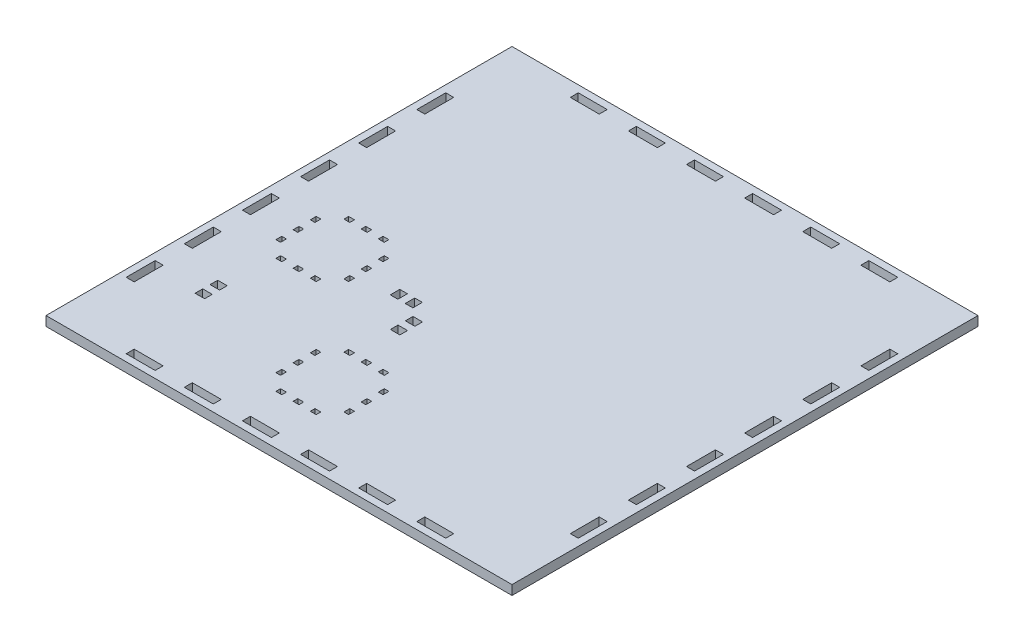
SolidWorks part; units mm, degrees
ref_plane "Front Plane" through (0, 0, 0) normal (0, 0, 1) x (1, 0, 0)
ref_plane "Top Plane" through (0, 0, 0) normal (0, 1, 0) x (1, 0, 0)
ref_plane "Right Plane" through (0, 0, 0) normal (1, 0, 0) x (0, 0, -1)
sketch "Sketch1" plane through (0, 0, 0) normal (0, 1, 0) x (1, 0, 0)
  line L182 (-7.5125, 303.9125) -> (303.8875, 303.9125)
  line L183 (-7.5125, 303.9125) -> (-7.5125, -7.4875)
  line L184 (-7.5125, -7.4875) -> (303.8875, -7.4875)
  line L185 (303.8875, 303.9125) -> (303.8875, -7.4875)
  line L195 (-2.9125, 60.7875) -> (2.4875, 60.7875)
  line L196 (-2.9125, 60.7875) -> (-2.9125, 41.3625)
  line L197 (-2.9125, 41.3625) -> (2.4875, 41.3625)
  line L198 (2.4875, 60.7875) -> (2.4875, 41.3625)
  line L200 (-2.9125, 99.6375) -> (2.4875, 99.6375)
  line L201 (-2.9125, 99.6375) -> (-2.9125, 80.2125)
  line L202 (-2.9125, 80.2125) -> (2.4875, 80.2125)
  line L203 (2.4875, 99.6375) -> (2.4875, 80.2125)
  line L205 (-2.9125, 138.4875) -> (2.4875, 138.4875)
  line L206 (-2.9125, 138.4875) -> (-2.9125, 119.0625)
  line L207 (-2.9125, 119.0625) -> (2.4875, 119.0625)
  line L208 (2.4875, 138.4875) -> (2.4875, 119.0625)
  line L211 (-2.9125, 177.3375) -> (2.4875, 177.3375)
  line L212 (-2.9125, 177.3375) -> (-2.9125, 157.9125)
  line L213 (-2.9125, 157.9125) -> (2.4875, 157.9125)
  line L214 (2.4875, 177.3375) -> (2.4875, 157.9125)
  line L216 (-2.9125, 216.1875) -> (2.4875, 216.1875)
  line L217 (-2.9125, 216.1875) -> (-2.9125, 196.7625)
  line L218 (-2.9125, 196.7625) -> (2.4875, 196.7625)
  line L219 (2.4875, 216.1875) -> (2.4875, 196.7625)
  line L221 (-2.9125, 255.0375) -> (2.4875, 255.0375)
  line L222 (-2.9125, 255.0375) -> (-2.9125, 235.6125)
  line L223 (-2.9125, 235.6125) -> (2.4875, 235.6125)
  line L224 (2.4875, 255.0375) -> (2.4875, 235.6125)
  line L236 (41.3625, 299.3125) -> (60.7875, 299.3125)
  line L237 (41.3625, 299.3125) -> (41.3625, 293.9125)
  line L238 (41.3625, 293.9125) -> (60.7875, 293.9125)
  line L239 (60.7875, 299.3125) -> (60.7875, 293.9125)
  line L241 (80.2125, 299.3125) -> (99.6375, 299.3125)
  line L242 (80.2125, 299.3125) -> (80.2125, 293.9125)
  line L243 (80.2125, 293.9125) -> (99.6375, 293.9125)
  line L244 (99.6375, 299.3125) -> (99.6375, 293.9125)
  line L246 (119.0625, 299.3125) -> (138.4875, 299.3125)
  line L247 (119.0625, 299.3125) -> (119.0625, 293.9125)
  line L248 (119.0625, 293.9125) -> (138.4875, 293.9125)
  line L249 (138.4875, 299.3125) -> (138.4875, 293.9125)
  line L251 (157.9125, 299.3125) -> (177.3375, 299.3125)
  line L252 (157.9125, 299.3125) -> (157.9125, 293.9125)
  line L253 (157.9125, 293.9125) -> (177.3375, 293.9125)
  line L254 (177.3375, 299.3125) -> (177.3375, 293.9125)
  line L256 (196.7625, 299.3125) -> (216.1875, 299.3125)
  line L257 (196.7625, 299.3125) -> (196.7625, 293.9125)
  line L258 (196.7625, 293.9125) -> (216.1875, 293.9125)
  line L259 (216.1875, 299.3125) -> (216.1875, 293.9125)
  line L260 (235.6125, 299.3125) -> (255.0375, 299.3125)
  line L261 (235.6125, 299.3125) -> (235.6125, 293.9125)
  line L262 (235.6125, 293.9125) -> (255.0375, 293.9125)
  line L263 (255.0375, 299.3125) -> (255.0375, 293.9125)
  line L272 (299.2875, 255.0625) -> (293.8875, 255.0625)
  line L273 (299.2875, 255.0625) -> (299.2875, 235.6375)
  line L274 (299.2875, 235.6375) -> (293.8875, 235.6375)
  line L275 (293.8875, 255.0625) -> (293.8875, 235.6375)
  line L276 (299.2875, 216.2125) -> (293.8875, 216.2125)
  line L277 (299.2875, 216.2125) -> (299.2875, 196.7875)
  line L278 (299.2875, 196.7875) -> (293.8875, 196.7875)
  line L279 (293.8875, 216.2125) -> (293.8875, 196.7875)
  line L280 (299.2875, 177.3625) -> (293.8875, 177.3625)
  line L281 (299.2875, 177.3625) -> (299.2875, 157.9375)
  line L282 (299.2875, 157.9375) -> (293.8875, 157.9375)
  line L283 (293.8875, 177.3625) -> (293.8875, 157.9375)
  line L284 (299.2875, 138.5125) -> (293.8875, 138.5125)
  line L285 (299.2875, 138.5125) -> (299.2875, 119.0875)
  line L286 (299.2875, 119.0875) -> (293.8875, 119.0875)
  line L287 (293.8875, 138.5125) -> (293.8875, 119.0875)
  line L288 (299.2875, 99.6625) -> (293.8875, 99.6625)
  line L289 (299.2875, 99.6625) -> (299.2875, 80.2375)
  line L290 (299.2875, 80.2375) -> (293.8875, 80.2375)
  line L291 (293.8875, 99.6625) -> (293.8875, 80.2375)
  line L292 (299.2875, 60.8125) -> (293.8875, 60.8125)
  line L293 (299.2875, 60.8125) -> (299.2875, 41.3875)
  line L294 (299.2875, 41.3875) -> (293.8875, 41.3875)
  line L295 (293.8875, 60.8125) -> (293.8875, 41.3875)
  line L304 (255.0125, 2.5125) -> (235.5875, 2.5125)
  line L305 (255.0125, 2.5125) -> (255.0125, -2.8875)
  line L306 (255.0125, -2.8875) -> (235.5875, -2.8875)
  line L307 (235.5875, 2.5125) -> (235.5875, -2.8875)
  line L308 (216.1625, 2.5125) -> (196.7375, 2.5125)
  line L309 (216.1625, 2.5125) -> (216.1625, -2.8875)
  line L310 (216.1625, -2.8875) -> (196.7375, -2.8875)
  line L311 (196.7375, 2.5125) -> (196.7375, -2.8875)
  line L312 (177.3125, 2.5125) -> (157.8875, 2.5125)
  line L313 (177.3125, 2.5125) -> (177.3125, -2.8875)
  line L314 (177.3125, -2.8875) -> (157.8875, -2.8875)
  line L315 (157.8875, 2.5125) -> (157.8875, -2.8875)
  line L316 (138.4625, 2.5125) -> (119.0375, 2.5125)
  line L317 (138.4625, 2.5125) -> (138.4625, -2.8875)
  line L318 (138.4625, -2.8875) -> (119.0375, -2.8875)
  line L319 (119.0375, 2.5125) -> (119.0375, -2.8875)
  line L320 (99.6125, 2.5125) -> (80.1875, 2.5125)
  line L321 (99.6125, 2.5125) -> (99.6125, -2.8875)
  line L322 (99.6125, -2.8875) -> (80.1875, -2.8875)
  line L323 (80.1875, 2.5125) -> (80.1875, -2.8875)
  line L324 (60.7625, 2.5125) -> (41.3375, 2.5125)
  line L325 (60.7625, 2.5125) -> (60.7625, -2.8875)
  line L326 (60.7625, -2.8875) -> (41.3375, -2.8875)
  line L327 (41.3375, 2.5125) -> (41.3375, -2.8875)
  line L528 (36.1625, 151.0125) -> (40.1625, 151.0125)
  line L529 (36.1625, 151.0125) -> (36.1625, 147.8375)
  line L530 (36.1625, 147.8375) -> (40.1625, 147.8375)
  line L531 (40.1625, 151.0125) -> (40.1625, 147.8375)
  line L532 (47.6625, 151.0125) -> (51.6625, 151.0125)
  line L533 (47.6625, 151.0125) -> (47.6625, 147.8375)
  line L534 (47.6625, 147.8375) -> (51.6625, 147.8375)
  line L535 (51.6625, 151.0125) -> (51.6625, 147.8375)
  line L536 (59.1625, 151.0125) -> (63.1625, 151.0125)
  line L537 (59.1625, 151.0125) -> (59.1625, 147.8375)
  line L538 (59.1625, 147.8375) -> (63.1625, 147.8375)
  line L539 (63.1625, 151.0125) -> (63.1625, 147.8375)
  line L540 (70.8125, 140.1875) -> (73.9875, 140.1875)
  line L541 (70.8125, 140.1875) -> (70.8125, 136.1875)
  line L542 (70.8125, 136.1875) -> (73.9875, 136.1875)
  line L543 (73.9875, 140.1875) -> (73.9875, 136.1875)
  line L544 (70.8125, 128.6875) -> (73.9875, 128.6875)
  line L545 (70.8125, 128.6875) -> (70.8125, 124.6875)
  line L546 (70.8125, 124.6875) -> (73.9875, 124.6875)
  line L547 (73.9875, 128.6875) -> (73.9875, 124.6875)
  line L548 (70.8125, 117.1875) -> (73.9875, 117.1875)
  line L549 (70.8125, 117.1875) -> (70.8125, 113.1875)
  line L550 (70.8125, 113.1875) -> (73.9875, 113.1875)
  line L551 (73.9875, 117.1875) -> (73.9875, 113.1875)
  line L552 (63.1625, 105.5375) -> (59.1625, 105.5375)
  line L553 (63.1625, 105.5375) -> (63.1625, 102.3625)
  line L554 (63.1625, 102.3625) -> (59.1625, 102.3625)
  line L555 (59.1625, 105.5375) -> (59.1625, 102.3625)
  line L556 (51.6625, 105.5375) -> (47.6625, 105.5375)
  line L557 (51.6625, 105.5375) -> (51.6625, 102.3625)
  line L558 (51.6625, 102.3625) -> (47.6625, 102.3625)
  line L559 (47.6625, 105.5375) -> (47.6625, 102.3625)
  line L560 (40.1625, 105.5375) -> (36.1625, 105.5375)
  line L561 (40.1625, 105.5375) -> (40.1625, 102.3625)
  line L562 (40.1625, 102.3625) -> (36.1625, 102.3625)
  line L563 (36.1625, 105.5375) -> (36.1625, 102.3625)
  line L564 (28.5125, 113.1875) -> (25.3375, 113.1875)
  line L565 (28.5125, 113.1875) -> (28.5125, 117.1875)
  line L566 (28.5125, 117.1875) -> (25.3375, 117.1875)
  line L567 (25.3375, 113.1875) -> (25.3375, 117.1875)
  line L568 (28.5125, 124.6875) -> (25.3375, 124.6875)
  line L569 (28.5125, 124.6875) -> (28.5125, 128.6875)
  line L570 (28.5125, 128.6875) -> (25.3375, 128.6875)
  line L571 (25.3375, 124.6875) -> (25.3375, 128.6875)
  line L572 (28.5125, 136.1875) -> (25.3375, 136.1875)
  line L573 (28.5125, 136.1875) -> (28.5125, 140.1875)
  line L574 (28.5125, 140.1875) -> (25.3375, 140.1875)
  line L575 (25.3375, 136.1875) -> (25.3375, 140.1875)
  line L576 (113.1625, 74.0125) -> (117.1625, 74.0125)
  line L577 (113.1625, 74.0125) -> (113.1625, 70.8375)
  line L578 (113.1625, 70.8375) -> (117.1625, 70.8375)
  line L579 (117.1625, 74.0125) -> (117.1625, 70.8375)
  line L580 (124.6625, 74.0125) -> (128.6625, 74.0125)
  line L581 (124.6625, 74.0125) -> (124.6625, 70.8375)
  line L582 (124.6625, 70.8375) -> (128.6625, 70.8375)
  line L583 (128.6625, 74.0125) -> (128.6625, 70.8375)
  line L584 (136.1625, 74.0125) -> (140.1625, 74.0125)
  line L585 (136.1625, 74.0125) -> (136.1625, 70.8375)
  line L586 (136.1625, 70.8375) -> (140.1625, 70.8375)
  line L587 (140.1625, 74.0125) -> (140.1625, 70.8375)
  line L588 (150.9875, 63.1875) -> (147.8125, 63.1875)
  line L589 (150.9875, 63.1875) -> (150.9875, 59.1875)
  line L590 (150.9875, 59.1875) -> (147.8125, 59.1875)
  line L591 (147.8125, 63.1875) -> (147.8125, 59.1875)
  line L592 (150.9875, 51.6875) -> (147.8125, 51.6875)
  line L593 (150.9875, 51.6875) -> (150.9875, 47.6875)
  line L594 (150.9875, 47.6875) -> (147.8125, 47.6875)
  line L595 (147.8125, 51.6875) -> (147.8125, 47.6875)
  line L596 (150.9875, 40.1875) -> (147.8125, 40.1875)
  line L597 (150.9875, 40.1875) -> (150.9875, 36.1875)
  line L598 (150.9875, 36.1875) -> (147.8125, 36.1875)
  line L599 (147.8125, 40.1875) -> (147.8125, 36.1875)
  line L600 (140.1625, 28.5375) -> (136.1625, 28.5375)
  line L601 (140.1625, 28.5375) -> (140.1625, 25.3625)
  line L602 (140.1625, 25.3625) -> (136.1625, 25.3625)
  line L603 (136.1625, 28.5375) -> (136.1625, 25.3625)
  line L604 (128.6625, 28.5375) -> (124.6625, 28.5375)
  line L605 (128.6625, 28.5375) -> (128.6625, 25.3625)
  line L606 (128.6625, 25.3625) -> (124.6625, 25.3625)
  line L607 (124.6625, 28.5375) -> (124.6625, 25.3625)
  line L608 (117.1625, 28.5375) -> (113.1625, 28.5375)
  line L609 (117.1625, 28.5375) -> (117.1625, 25.3625)
  line L610 (117.1625, 25.3625) -> (113.1625, 25.3625)
  line L611 (113.1625, 28.5375) -> (113.1625, 25.3625)
  line L612 (105.5125, 36.1875) -> (102.3375, 36.1875)
  line L613 (105.5125, 36.1875) -> (105.5125, 40.1875)
  line L614 (105.5125, 40.1875) -> (102.3375, 40.1875)
  line L615 (102.3375, 36.1875) -> (102.3375, 40.1875)
  line L616 (105.5125, 47.6875) -> (102.3375, 47.6875)
  line L617 (105.5125, 47.6875) -> (105.5125, 51.6875)
  line L618 (105.5125, 51.6875) -> (102.3375, 51.6875)
  line L619 (102.3375, 47.6875) -> (102.3375, 51.6875)
  line L620 (105.5125, 59.1875) -> (102.3375, 59.1875)
  line L621 (105.5125, 59.1875) -> (105.5125, 63.1875)
  line L622 (105.5125, 63.1875) -> (102.3375, 63.1875)
  line L623 (102.3375, 59.1875) -> (102.3375, 63.1875)
  dimension "D1" = 311.4
  dimension "D3" = 311.4
extrude "Boss-Extrude4" add sketch "Sketch1" along normal blind 6.35
sketch "Sketch4" plane through (0, 6.35, 0) normal (0, 1, 0) x (1, 0, 0)
  line L0 (303.8875, 303.9125) -> (-7.5125, 303.9125) construction
  line B0 (41.3375, 2.5125) -> (60.7625, 2.5125)
  line B1 (2.4875, 2.5125) -> (21.9125, 2.5125)
  line B2 (2.4875, 2.5125) -> (2.4875, -2.8875)
  line B3 (2.4875, -2.8875) -> (21.9125, -2.8875)
  line B4 (21.9125, 2.5125) -> (21.9125, -2.8875)
  line B5 (41.3375, 2.5125) -> (41.3375, -2.8875)
  line B6 (41.3375, -2.8875) -> (60.7625, -2.8875)
  line B7 (60.7625, 2.5125) -> (60.7625, -2.8875)
  line B8 (80.1875, 2.5125) -> (99.6125, 2.5125)
  line B9 (80.1875, 2.5125) -> (80.1875, -2.8875)
  line B10 (80.1875, -2.8875) -> (99.6125, -2.8875)
  line B11 (99.6125, 2.5125) -> (99.6125, -2.8875)
  line B12 (119.0375, 2.5125) -> (138.4625, 2.5125)
  line B13 (119.0375, 2.5125) -> (119.0375, -2.8875)
  line B14 (119.0375, -2.8875) -> (138.4625, -2.8875)
  line B15 (138.4625, 2.5125) -> (138.4625, -2.8875)
  line B16 (157.8875, 2.5125) -> (177.3125, 2.5125)
  line B17 (157.8875, 2.5125) -> (157.8875, -2.8875)
  line B18 (157.8875, -2.8875) -> (177.3125, -2.8875)
  line B19 (177.3125, 2.5125) -> (177.3125, -2.8875)
  line B20 (196.7375, 2.5125) -> (216.1625, 2.5125)
  line B21 (196.7375, 2.5125) -> (196.7375, -2.8875)
  line B22 (196.7375, -2.8875) -> (216.1625, -2.8875)
  line B23 (216.1625, 2.5125) -> (216.1625, -2.8875)
  line B24 (235.5875, 2.5125) -> (255.0125, 2.5125)
  line B25 (235.5875, 2.5125) -> (235.5875, -2.8875)
  line B26 (235.5875, -2.8875) -> (255.0125, -2.8875)
  line B27 (255.0125, 2.5125) -> (255.0125, -2.8875)
  line B28 (274.4375, 2.5125) -> (293.8625, 2.5125)
  line B29 (274.4375, 2.5125) -> (274.4375, -2.8875)
  line B30 (274.4375, -2.8875) -> (293.8625, -2.8875)
  line B31 (293.8625, 2.5125) -> (293.8625, -2.8875)
  line B32 (-2.9125, 60.7875) -> (2.4875, 60.7875)
  line B33 (-2.9125, 2.5125) -> (2.4875, 2.5125)
  line B34 (-2.9125, 2.5125) -> (-2.9125, 21.9375)
  line B35 (-2.9125, 21.9375) -> (2.4875, 21.9375)
  line B36 (2.4875, 2.5125) -> (2.4875, 21.9375)
  line B37 (2.4875, 41.3625) -> (2.4875, 60.7875)
  line B38 (-2.9125, 41.3625) -> (-2.9125, 60.7875)
  line B39 (-2.9125, 41.3625) -> (2.4875, 41.3625)
  line B40 (-2.9125, 99.6375) -> (2.4875, 99.6375)
  line B41 (2.4875, 80.2125) -> (2.4875, 99.6375)
  line B42 (-2.9125, 80.2125) -> (-2.9125, 99.6375)
  line B43 (-2.9125, 80.2125) -> (2.4875, 80.2125)
  line B44 (-2.9125, 138.4875) -> (2.4875, 138.4875)
  line B45 (2.4875, 119.0625) -> (2.4875, 138.4875)
  line B46 (-2.9125, 119.0625) -> (-2.9125, 138.4875)
  line B47 (-2.9125, 119.0625) -> (2.4875, 119.0625)
  line B48 (-2.9125, 177.3375) -> (2.4875, 177.3375)
  line B49 (2.4875, 157.9125) -> (2.4875, 177.3375)
  line B50 (-2.9125, 157.9125) -> (-2.9125, 177.3375)
  line B51 (-2.9125, 157.9125) -> (2.4875, 157.9125)
  line B52 (-2.9125, 216.1875) -> (2.4875, 216.1875)
  line B53 (2.4875, 196.7625) -> (2.4875, 216.1875)
  line B54 (-2.9125, 196.7625) -> (-2.9125, 216.1875)
  line B55 (-2.9125, 196.7625) -> (2.4875, 196.7625)
  line B56 (-2.9125, 255.0375) -> (2.4875, 255.0375)
  line B57 (2.4875, 235.6125) -> (2.4875, 255.0375)
  line B58 (-2.9125, 235.6125) -> (-2.9125, 255.0375)
  line B59 (-2.9125, 235.6125) -> (2.4875, 235.6125)
  line B60 (-2.9125, 293.8875) -> (2.4875, 293.8875)
  line B61 (2.4875, 274.4625) -> (2.4875, 293.8875)
  line B62 (-2.9125, 274.4625) -> (-2.9125, 293.8875)
  line B63 (-2.9125, 274.4625) -> (2.4875, 274.4625)
  line B64 (-7.5125, 303.9125) -> (303.8875, -7.4875) construction
  line B65 (21.9375, 299.3125) -> (21.9375, 293.9125)
  line B66 (21.9375, 299.3125) -> (2.5125, 299.3125)
  line B67 (21.9375, 293.9125) -> (2.5125, 293.9125)
  line B68 (2.5125, 299.3125) -> (2.5125, 293.9125)
  line B69 (60.7875, 299.3125) -> (60.7875, 293.9125)
  line B70 (60.7875, 299.3125) -> (41.3625, 299.3125)
  line B71 (60.7875, 293.9125) -> (41.3625, 293.9125)
  line B72 (41.3625, 299.3125) -> (41.3625, 293.9125)
  line B73 (99.6375, 299.3125) -> (99.6375, 293.9125)
  line B74 (99.6375, 299.3125) -> (80.2125, 299.3125)
  line B75 (99.6375, 293.9125) -> (80.2125, 293.9125)
  line B76 (80.2125, 299.3125) -> (80.2125, 293.9125)
  line B77 (138.4875, 299.3125) -> (138.4875, 293.9125)
  line B78 (138.4875, 299.3125) -> (119.0625, 299.3125)
  line B79 (138.4875, 293.9125) -> (119.0625, 293.9125)
  line B80 (119.0625, 299.3125) -> (119.0625, 293.9125)
  line B81 (177.3375, 299.3125) -> (177.3375, 293.9125)
  line B82 (177.3375, 299.3125) -> (157.9125, 299.3125)
  line B83 (177.3375, 293.9125) -> (157.9125, 293.9125)
  line B84 (157.9125, 299.3125) -> (157.9125, 293.9125)
  line B85 (216.1875, 299.3125) -> (216.1875, 293.9125)
  line B86 (216.1875, 299.3125) -> (196.7625, 299.3125)
  line B87 (216.1875, 293.9125) -> (196.7625, 293.9125)
  line B88 (196.7625, 299.3125) -> (196.7625, 293.9125)
  line B89 (255.0375, 299.3125) -> (255.0375, 293.9125)
  line B90 (255.0375, 299.3125) -> (235.6125, 299.3125)
  line B91 (255.0375, 293.9125) -> (235.6125, 293.9125)
  line B92 (293.8875, 293.9125) -> (274.4625, 293.9125)
  line B93 (274.4625, 299.3125) -> (274.4625, 293.9125)
  line B94 (293.8875, 299.3125) -> (274.4625, 299.3125)
  line B95 (293.8875, 299.3125) -> (293.8875, 293.9125)
  line B96 (235.6125, 299.3125) -> (235.6125, 293.9125)
  line B97 (293.8875, 2.5375) -> (299.2875, 2.5375)
  line B98 (299.2875, 21.9625) -> (299.2875, 2.5375)
  line B99 (293.8875, 21.9625) -> (299.2875, 21.9625)
  line B100 (293.8875, 21.9625) -> (293.8875, 2.5375)
  line B101 (293.8875, 41.3875) -> (299.2875, 41.3875)
  line B102 (299.2875, 60.8125) -> (299.2875, 41.3875)
  line B103 (293.8875, 60.8125) -> (299.2875, 60.8125)
  line B104 (293.8875, 60.8125) -> (293.8875, 41.3875)
  line B105 (293.8875, 80.2375) -> (299.2875, 80.2375)
  line B106 (299.2875, 99.6625) -> (299.2875, 80.2375)
  line B107 (293.8875, 99.6625) -> (299.2875, 99.6625)
  line B108 (293.8875, 99.6625) -> (293.8875, 80.2375)
  line B109 (293.8875, 119.0875) -> (299.2875, 119.0875)
  line B110 (299.2875, 138.5125) -> (299.2875, 119.0875)
  line B111 (293.8875, 138.5125) -> (299.2875, 138.5125)
  line B112 (293.8875, 138.5125) -> (293.8875, 119.0875)
  line B113 (293.8875, 157.9375) -> (299.2875, 157.9375)
  line B114 (299.2875, 177.3625) -> (299.2875, 157.9375)
  line B115 (293.8875, 177.3625) -> (299.2875, 177.3625)
  line B116 (293.8875, 177.3625) -> (293.8875, 157.9375)
  line B117 (293.8875, 196.7875) -> (299.2875, 196.7875)
  line B118 (299.2875, 216.2125) -> (299.2875, 196.7875)
  line B119 (293.8875, 216.2125) -> (299.2875, 216.2125)
  line B120 (293.8875, 216.2125) -> (293.8875, 196.7875)
  line B121 (293.8875, 235.6375) -> (299.2875, 235.6375)
  line B122 (299.2875, 255.0625) -> (299.2875, 235.6375)
  line B123 (293.8875, 255.0625) -> (299.2875, 255.0625)
  line B124 (293.8875, 274.4875) -> (299.2875, 274.4875)
  line B125 (299.2875, 293.9125) -> (299.2875, 274.4875)
  line B126 (293.8875, 293.9125) -> (299.2875, 293.9125)
  line B127 (293.8875, 293.9125) -> (293.8875, 274.4875)
  line B128 (293.8875, 255.0625) -> (293.8875, 235.6375)
  line B129 (2.5125, 293.9125) -> (2.4875, 293.8875)
  line B130 (293.8875, 2.5375) -> (293.8625, 2.5125)
  line B131 (35.6625, 260.7375) -> (115.6625, 260.7375)
  line B132 (35.6625, 260.7375) -> (35.6625, 180.7375)
  line B133 (35.6625, 180.7375) -> (115.6625, 180.7375)
  line B134 (115.6625, 260.7375) -> (115.6625, 180.7375)
  arc B135 (-2.9125, 293.8875) -> (2.5125, 299.2874) centre (2.4875, 293.8875) cw
  arc B136 (293.8625, -2.8875) -> (299.2624, 2.5375) centre (293.8625, 2.5125) ccw
  arc B137 (299.2875, 293.9125) -> (293.8875, 299.3125) centre (293.8875, 293.9125) ccw
  arc B138 (2.4875, -2.8875) -> (-2.9125, 2.5125) centre (2.4875, 2.5125) cw
sketch_block_instance "Outer Mounting Holes-4"
sketch_block "Outer Mounting Holes" parameters "D1"=5.4, "D2"=19.425, "D3"=19.425, "D4"=19.425, "D5"=80, "D6"=302.2
extrude "Cut-Extrude3" cut sketch "Sketch4" against normal blind 6.35 contours B66 B68 B67 B65 | B62 B63 B61 B60 | B135 B60 B129 B68 | B126 B137 B95 | B95 B94 B93 B92 | B126 B127 B124 B125 | B33 B36 B35 B34 | B4 B1 B2 B3 | B138 B2 B33 | B31 B136 B97 B130 | B31 B28 B29 B30 | B99 B100 B97 B98
sketch "Sketch5" plane through (0, 6.35, 0) normal (0, 1, 0) x (1, 0, 0)
  line L8 (254.9969, 293.9531) -> (254.9969, 299.2719)
  line L9 (235.6531, 293.9531) -> (254.9969, 293.9531)
  line L10 (235.6531, 299.2719) -> (235.6531, 293.9531)
  line L11 (254.9969, 299.2719) -> (235.6531, 299.2719)
  line L12 (254.9969, 293.9531) -> (254.9969, 299.2719)
  line L13 (235.6531, 293.9531) -> (254.9969, 293.9531)
  line L14 (235.6531, 299.2719) -> (235.6531, 293.9531)
  line L15 (254.9969, 299.2719) -> (235.6531, 299.2719)
  line L16 (-7.5531, -7.5281) -> (303.9281, -7.5281)
  line L17 (303.9281, -7.5281) -> (303.9281, 303.9531)
  line L18 (-7.5531, 303.9531) -> (-7.5531, -7.5281)
  line L19 (303.9281, 303.9531) -> (-7.5531, 303.9531)
  line L20 (-7.5531, -7.5281) -> (303.9281, -7.5281)
  line L21 (303.9281, -7.5281) -> (303.9281, 303.9531)
  line L22 (-7.5531, 303.9531) -> (-7.5531, -7.5281)
  line L23 (303.9281, 303.9531) -> (-7.5531, 303.9531)
  line L24 (293.8625, -2.8469) -> (274.4781, -2.8469)
  line L25 (274.4781, -2.8469) -> (274.4781, 2.4719)
  line L26 (274.4781, 2.4719) -> (293.8625, 2.4719)
  line L27 (293.8625, -2.8469) -> (274.4781, -2.8469)
  line L28 (274.5031, 299.2719) -> (293.8875, 299.2719)
  line L29 (274.5031, 293.9531) -> (274.5031, 299.2719)
  line L30 (293.8875, 293.9531) -> (274.5031, 293.9531)
  line L31 (274.5031, 299.2719) -> (293.8875, 299.2719)
  line L32 (274.5031, 293.9531) -> (274.5031, 299.2719)
  line L33 (293.8875, 293.9531) -> (274.5031, 293.9531)
  line L34 (299.2469, 41.4281) -> (299.2469, 60.7719)
  line L35 (293.9281, 196.8281) -> (299.2469, 196.8281)
  line L36 (293.9281, 216.1719) -> (293.9281, 196.8281)
  line L37 (299.2469, 196.8281) -> (299.2469, 216.1719)
  line L38 (299.2469, 216.1719) -> (293.9281, 216.1719)
  line L39 (293.9281, 196.8281) -> (299.2469, 196.8281)
  line L40 (293.9281, 274.5281) -> (299.2469, 274.5281)
  line L41 (299.2469, 274.5281) -> (299.2469, 293.9125)
  line L42 (293.9281, 293.9125) -> (293.9281, 274.5281)
  line L43 (293.9281, 274.5281) -> (299.2469, 274.5281)
  line L44 (299.2469, 274.5281) -> (299.2469, 293.9125)
  line L45 (293.9281, 293.9125) -> (293.9281, 274.5281)
  line L46 (293.9281, 216.1719) -> (293.9281, 196.8281)
  line L47 (299.2469, 196.8281) -> (299.2469, 216.1719)
  line L48 (299.2469, 216.1719) -> (293.9281, 216.1719)
  line L49 (293.9281, 41.4281) -> (299.2469, 41.4281)
  line L50 (293.9281, 60.7719) -> (293.9281, 41.4281)
  line L51 (299.2469, 60.7719) -> (293.9281, 60.7719)
  line L52 (299.2469, 41.4281) -> (299.2469, 60.7719)
  line L53 (293.9281, 41.4281) -> (299.2469, 41.4281)
  line L54 (293.9281, 60.7719) -> (293.9281, 41.4281)
  line L55 (299.2469, 60.7719) -> (293.9281, 60.7719)
  line L56 (274.4781, -2.8469) -> (274.4781, 2.4719)
  line L57 (293.9281, 235.6781) -> (299.2469, 235.6781)
  line L58 (299.2469, 235.6781) -> (299.2469, 255.0219)
  line L59 (299.2469, 255.0219) -> (293.9281, 255.0219)
  line L60 (293.9281, 255.0219) -> (293.9281, 235.6781)
  line L61 (293.9281, 235.6781) -> (299.2469, 235.6781)
  line L62 (299.2469, 235.6781) -> (299.2469, 255.0219)
  line L63 (299.2469, 255.0219) -> (293.9281, 255.0219)
  line L64 (293.9281, 255.0219) -> (293.9281, 235.6781)
  line L65 (274.4781, 2.4719) -> (293.8625, 2.4719)
  line L70 (299.2469, 157.9781) -> (299.2469, 177.3219)
  line L71 (293.9281, 177.3219) -> (293.9281, 157.9781)
  line L72 (293.9281, 157.9781) -> (299.2469, 157.9781)
  line L73 (21.8969, 293.9531) -> (21.8969, 299.2719)
  line L74 (2.5125, 293.9531) -> (21.8969, 293.9531)
  line L75 (21.8969, 299.2719) -> (2.5125, 299.2719)
  line L76 (21.8969, 293.9531) -> (21.8969, 299.2719)
  line L77 (2.5125, 293.9531) -> (21.8969, 293.9531)
  line L78 (21.8969, 299.2719) -> (2.5125, 299.2719)
  line L79 (299.2469, 177.3219) -> (293.9281, 177.3219)
  line L80 (299.2469, 157.9781) -> (299.2469, 177.3219)
  line L81 (293.9281, 177.3219) -> (293.9281, 157.9781)
  line L82 (293.9281, 157.9781) -> (299.2469, 157.9781)
  line L83 (299.2469, 177.3219) -> (293.9281, 177.3219)
  line L85 (-2.8719, 274.5031) -> (2.4469, 274.5031)
  line L86 (-2.8719, 293.8875) -> (-2.8719, 274.5031)
  line L87 (2.4469, 274.5031) -> (2.4469, 293.8875)
  line L88 (-2.8719, 274.5031) -> (2.4469, 274.5031)
  line L89 (-2.8719, 293.8875) -> (-2.8719, 274.5031)
  line L90 (2.4469, 274.5031) -> (2.4469, 293.8875)
  line L91 (-2.8719, 157.9531) -> (2.4469, 157.9531)
  line L92 (216.1219, -2.8469) -> (216.1219, 2.4719)
  line L93 (-2.8719, 177.2969) -> (-2.8719, 157.9531)
  line L94 (196.7781, 2.4719) -> (196.7781, -2.8469)
  line L95 (196.7781, -2.8469) -> (216.1219, -2.8469)
  line L96 (216.1219, 2.4719) -> (196.7781, 2.4719)
  line L97 (254.9719, -2.8469) -> (254.9719, 2.4719)
  line L98 (235.6281, 2.4719) -> (235.6281, -2.8469)
  line L99 (235.6281, -2.8469) -> (254.9719, -2.8469)
  line L100 (299.2469, 119.1281) -> (299.2469, 138.4719)
  line L101 (293.9281, 138.4719) -> (293.9281, 119.1281)
  line L102 (60.7469, 293.9531) -> (60.7469, 299.2719)
  line L103 (41.4031, 293.9531) -> (60.7469, 293.9531)
  line L104 (41.4031, 299.2719) -> (41.4031, 293.9531)
  line L105 (60.7469, 299.2719) -> (41.4031, 299.2719)
  line L106 (60.7469, 293.9531) -> (60.7469, 299.2719)
  line L107 (41.4031, 293.9531) -> (60.7469, 293.9531)
  line L108 (41.4031, 299.2719) -> (41.4031, 293.9531)
  line L109 (60.7469, 299.2719) -> (41.4031, 299.2719)
  line L110 (293.9281, 119.1281) -> (299.2469, 119.1281)
  line L111 (299.2469, 138.4719) -> (293.9281, 138.4719)
  line L112 (299.2469, 119.1281) -> (299.2469, 138.4719)
  line L113 (293.9281, 138.4719) -> (293.9281, 119.1281)
  line L114 (293.9281, 119.1281) -> (299.2469, 119.1281)
  line L115 (299.2469, 138.4719) -> (293.9281, 138.4719)
  line L116 (254.9719, 2.4719) -> (235.6281, 2.4719)
  line L117 (254.9719, -2.8469) -> (254.9719, 2.4719)
  line L118 (235.6281, 2.4719) -> (235.6281, -2.8469)
  line L119 (235.6281, -2.8469) -> (254.9719, -2.8469)
  line L120 (254.9719, 2.4719) -> (235.6281, 2.4719)
  line L121 (216.1219, -2.8469) -> (216.1219, 2.4719)
  line L122 (196.7781, 2.4719) -> (196.7781, -2.8469)
  line L123 (196.7781, -2.8469) -> (216.1219, -2.8469)
  line L124 (99.5969, 293.9531) -> (99.5969, 299.2719)
  line L125 (80.2531, 299.2719) -> (80.2531, 293.9531)
  line L126 (80.2531, 293.9531) -> (99.5969, 293.9531)
  line L127 (99.5969, 299.2719) -> (80.2531, 299.2719)
  line L128 (99.5969, 293.9531) -> (99.5969, 299.2719)
  line L129 (80.2531, 299.2719) -> (80.2531, 293.9531)
  line L130 (80.2531, 293.9531) -> (99.5969, 293.9531)
  line L131 (99.5969, 299.2719) -> (80.2531, 299.2719)
  line L132 (216.1219, 2.4719) -> (196.7781, 2.4719)
  line L133 (2.4469, 157.9531) -> (2.4469, 177.2969)
  line L134 (299.2469, 80.2781) -> (299.2469, 99.6219)
  line L135 (293.9281, 80.2781) -> (299.2469, 80.2781)
  line L136 (293.9281, 99.6219) -> (293.9281, 80.2781)
  line L137 (299.2469, 99.6219) -> (293.9281, 99.6219)
  line L138 (299.2469, 80.2781) -> (299.2469, 99.6219)
  line L139 (293.9281, 80.2781) -> (299.2469, 80.2781)
  line L140 (293.9281, 99.6219) -> (293.9281, 80.2781)
  line L141 (299.2469, 99.6219) -> (293.9281, 99.6219)
  line L142 (119.1031, 299.2719) -> (119.1031, 293.9531)
  line L143 (138.4469, 293.9531) -> (138.4469, 299.2719)
  line L144 (119.1031, 293.9531) -> (138.4469, 293.9531)
  line L145 (138.4469, 299.2719) -> (119.1031, 299.2719)
  line L146 (119.1031, 299.2719) -> (119.1031, 293.9531)
  line L147 (138.4469, 293.9531) -> (138.4469, 299.2719)
  line L148 (119.1031, 293.9531) -> (138.4469, 293.9531)
  line L149 (138.4469, 299.2719) -> (119.1031, 299.2719)
  line L150 (2.4469, 177.2969) -> (-2.8719, 177.2969)
  line L151 (-2.8719, 157.9531) -> (2.4469, 157.9531)
  line L152 (-2.8719, 177.2969) -> (-2.8719, 157.9531)
  line L153 (2.4469, 157.9531) -> (2.4469, 177.2969)
  line L154 (2.4469, 177.2969) -> (-2.8719, 177.2969)
  line L155 (-2.8719, 235.6531) -> (2.4469, 235.6531)
  line L156 (2.4469, 235.6531) -> (2.4469, 254.9969)
  line L157 (-2.8719, 254.9969) -> (-2.8719, 235.6531)
  line L158 (2.4469, 254.9969) -> (-2.8719, 254.9969)
  line L159 (177.2719, -2.8469) -> (177.2719, 2.4719)
  line L160 (157.9531, 299.2719) -> (157.9531, 293.9531)
  line L161 (177.2969, 293.9531) -> (177.2969, 299.2719)
  line L162 (157.9531, 293.9531) -> (177.2969, 293.9531)
  line L163 (177.2969, 299.2719) -> (157.9531, 299.2719)
  line L164 (157.9531, 299.2719) -> (157.9531, 293.9531)
  line L165 (177.2969, 293.9531) -> (177.2969, 299.2719)
  line L166 (157.9531, 293.9531) -> (177.2969, 293.9531)
  line L167 (177.2969, 299.2719) -> (157.9531, 299.2719)
  line L168 (157.9281, 2.4719) -> (157.9281, -2.8469)
  line L169 (157.9281, -2.8469) -> (177.2719, -2.8469)
  line L170 (299.2469, 2.5375) -> (299.2469, 21.9219)
  line L171 (299.2469, 21.9219) -> (293.9281, 21.9219)
  line L172 (293.9281, 21.9219) -> (293.9281, 2.5375)
  line L173 (299.2469, 2.5375) -> (299.2469, 21.9219)
  line L174 (299.2469, 21.9219) -> (293.9281, 21.9219)
  line L175 (293.9281, 21.9219) -> (293.9281, 2.5375)
  line L176 (177.2719, 2.4719) -> (157.9281, 2.4719)
  line L177 (177.2719, -2.8469) -> (177.2719, 2.4719)
  line L178 (157.9281, 2.4719) -> (157.9281, -2.8469)
  line L179 (157.9281, -2.8469) -> (177.2719, -2.8469)
  line L180 (196.8031, 299.2719) -> (196.8031, 293.9531)
  line L181 (216.1469, 293.9531) -> (216.1469, 299.2719)
  line L182 (216.1469, 299.2719) -> (196.8031, 299.2719)
  line L183 (196.8031, 293.9531) -> (216.1469, 293.9531)
  line L184 (196.8031, 299.2719) -> (196.8031, 293.9531)
  line L185 (216.1469, 293.9531) -> (216.1469, 299.2719)
  line L186 (216.1469, 299.2719) -> (196.8031, 299.2719)
  line L187 (196.8031, 293.9531) -> (216.1469, 293.9531)
  line L188 (177.2719, 2.4719) -> (157.9281, 2.4719)
  line L189 (-2.8719, 235.6531) -> (2.4469, 235.6531)
  line L190 (2.4469, 235.6531) -> (2.4469, 254.9969)
  line L194 (-2.8719, 254.9969) -> (-2.8719, 235.6531)
  line L195 (-2.8719, 196.8031) -> (2.4469, 196.8031)
  line L196 (2.4469, 196.8031) -> (2.4469, 216.1469)
  line L197 (-2.8719, 216.1469) -> (-2.8719, 196.8031)
  line L198 (2.4469, 216.1469) -> (-2.8719, 216.1469)
  line L199 (138.4219, 2.4719) -> (119.0781, 2.4719)
  line L200 (119.0781, -2.8469) -> (138.4219, -2.8469)
  line L201 (138.4219, -2.8469) -> (138.4219, 2.4719)
  line L202 (119.0781, 2.4719) -> (119.0781, -2.8469)
  line L203 (138.4219, 2.4719) -> (119.0781, 2.4719)
  line L204 (119.0781, -2.8469) -> (138.4219, -2.8469)
  line L205 (138.4219, -2.8469) -> (138.4219, 2.4719)
  line L206 (119.0781, 2.4719) -> (119.0781, -2.8469)
  line L207 (-2.8719, 196.8031) -> (2.4469, 196.8031)
  line L208 (2.4469, 196.8031) -> (2.4469, 216.1469)
  line L209 (-2.8719, 216.1469) -> (-2.8719, 196.8031)
  line L210 (2.4469, 216.1469) -> (-2.8719, 216.1469)
  line L211 (2.4469, 254.9969) -> (-2.8719, 254.9969)
  line L212 (51.6219, 147.8781) -> (51.6219, 150.9719)
  line L213 (47.7031, 147.8781) -> (51.6219, 147.8781)
  line L214 (47.7031, 150.9719) -> (47.7031, 147.8781)
  line L215 (51.6219, 150.9719) -> (47.7031, 150.9719)
  line L216 (51.6219, 147.8781) -> (51.6219, 150.9719)
  line L217 (80.2281, 2.4719) -> (80.2281, -2.8469)
  line L218 (99.5719, -2.8469) -> (99.5719, 2.4719)
  line L219 (80.2281, -2.8469) -> (99.5719, -2.8469)
  line L220 (99.5719, 2.4719) -> (80.2281, 2.4719)
  line L221 (80.2281, 2.4719) -> (80.2281, -2.8469)
  line L222 (99.5719, -2.8469) -> (99.5719, 2.4719)
  line L223 (80.2281, -2.8469) -> (99.5719, -2.8469)
  line L224 (99.5719, 2.4719) -> (80.2281, 2.4719)
  line L225 (47.7031, 147.8781) -> (51.6219, 147.8781)
  line L226 (47.7031, 150.9719) -> (47.7031, 147.8781)
  line L227 (51.6219, 150.9719) -> (47.7031, 150.9719)
  line L228 (63.1219, 147.8781) -> (63.1219, 150.9719)
  line L229 (59.2031, 147.8781) -> (63.1219, 147.8781)
  line L230 (59.2031, 150.9719) -> (59.2031, 147.8781)
  line L231 (63.1219, 150.9719) -> (59.2031, 150.9719)
  line L232 (63.1219, 147.8781) -> (63.1219, 150.9719)
  line L233 (59.2031, 147.8781) -> (63.1219, 147.8781)
  line L234 (59.2031, 150.9719) -> (59.2031, 147.8781)
  line L235 (41.3781, 2.4719) -> (41.3781, -2.8469)
  line L236 (60.7219, -2.8469) -> (60.7219, 2.4719)
  line L237 (41.3781, -2.8469) -> (60.7219, -2.8469)
  line L238 (60.7219, 2.4719) -> (41.3781, 2.4719)
  line L239 (41.3781, 2.4719) -> (41.3781, -2.8469)
  line L240 (60.7219, -2.8469) -> (60.7219, 2.4719)
  line L241 (41.3781, -2.8469) -> (60.7219, -2.8469)
  line L242 (60.7219, 2.4719) -> (41.3781, 2.4719)
  line L243 (63.1219, 150.9719) -> (59.2031, 150.9719)
  line L248 (21.8719, 2.4719) -> (21.8719, -2.8469)
  line L249 (21.8719, -2.8469) -> (2.4875, -2.8469)
  line L250 (2.4875, 2.4719) -> (21.8719, 2.4719)
  line L251 (21.8719, 2.4719) -> (21.8719, -2.8469)
  line L252 (21.8719, -2.8469) -> (2.4875, -2.8469)
  line L253 (2.4875, 2.4719) -> (21.8719, 2.4719)
  line L260 (2.4469, 21.8969) -> (2.4469, 2.5125)
  line L261 (-2.8719, 2.5125) -> (-2.8719, 21.8969)
  line L262 (-2.8719, 21.8969) -> (2.4469, 21.8969)
  line L263 (2.4469, 21.8969) -> (2.4469, 2.5125)
  line L264 (-2.8719, 2.5125) -> (-2.8719, 21.8969)
  line L265 (-2.8719, 21.8969) -> (2.4469, 21.8969)
  line L266 (40.1219, 147.8781) -> (40.1219, 150.9719)
  line L267 (36.2031, 147.8781) -> (40.1219, 147.8781)
  line L268 (36.2031, 150.9719) -> (36.2031, 147.8781)
  line L269 (40.1219, 150.9719) -> (36.2031, 150.9719)
  line L270 (40.1219, 147.8781) -> (40.1219, 150.9719)
  line L271 (36.2031, 147.8781) -> (40.1219, 147.8781)
  line L272 (36.2031, 150.9719) -> (36.2031, 147.8781)
  line L273 (40.1219, 150.9719) -> (36.2031, 150.9719)
  line L277 (-2.8719, 41.4031) -> (2.4469, 41.4031)
  line L278 (2.4469, 41.4031) -> (2.4469, 60.7469)
  line L279 (-2.8719, 60.7469) -> (-2.8719, 41.4031)
  line L280 (2.4469, 60.7469) -> (-2.8719, 60.7469)
  line L281 (-2.8719, 41.4031) -> (2.4469, 41.4031)
  line L282 (2.4469, 41.4031) -> (2.4469, 60.7469)
  line L283 (-2.8719, 60.7469) -> (-2.8719, 41.4031)
  line L284 (2.4469, 60.7469) -> (-2.8719, 60.7469)
  line L292 (28.4719, 136.2281) -> (28.4719, 140.1469)
  line L293 (25.3781, 140.1469) -> (25.3781, 136.2281)
  line L294 (25.3781, 136.2281) -> (28.4719, 136.2281)
  line L295 (-2.8719, 80.2531) -> (2.4469, 80.2531)
  line L296 (-2.8719, 99.5969) -> (-2.8719, 80.2531)
  line L297 (2.4469, 80.2531) -> (2.4469, 99.5969)
  line L298 (2.4469, 99.5969) -> (-2.8719, 99.5969)
  line L299 (-2.8719, 80.2531) -> (2.4469, 80.2531)
  line L300 (-2.8719, 99.5969) -> (-2.8719, 80.2531)
  line L301 (2.4469, 80.2531) -> (2.4469, 99.5969)
  line L302 (2.4469, 99.5969) -> (-2.8719, 99.5969)
  line L303 (28.4719, 140.1469) -> (25.3781, 140.1469)
  line L304 (28.4719, 136.2281) -> (28.4719, 140.1469)
  line L305 (25.3781, 140.1469) -> (25.3781, 136.2281)
  line L306 (25.3781, 136.2281) -> (28.4719, 136.2281)
  line L307 (28.4719, 140.1469) -> (25.3781, 140.1469)
  line L313 (-2.8719, 119.1031) -> (2.4469, 119.1031)
  line L314 (2.4469, 119.1031) -> (2.4469, 138.4469)
  line L315 (-2.8719, 138.4469) -> (-2.8719, 119.1031)
  line L316 (2.4469, 138.4469) -> (-2.8719, 138.4469)
  line L317 (-2.8719, 119.1031) -> (2.4469, 119.1031)
  line L318 (2.4469, 119.1031) -> (2.4469, 138.4469)
  line L319 (-2.8719, 138.4469) -> (-2.8719, 119.1031)
  line L320 (2.4469, 138.4469) -> (-2.8719, 138.4469)
  line L326 (28.4719, 124.7281) -> (28.4719, 128.6469)
  line L327 (25.3781, 128.6469) -> (25.3781, 124.7281)
  line L328 (25.3781, 124.7281) -> (28.4719, 124.7281)
  line L329 (28.4719, 128.6469) -> (25.3781, 128.6469)
  line L330 (28.4719, 124.7281) -> (28.4719, 128.6469)
  line L331 (25.3781, 128.6469) -> (25.3781, 124.7281)
  line L332 (25.3781, 124.7281) -> (28.4719, 124.7281)
  line L333 (28.4719, 128.6469) -> (25.3781, 128.6469)
  line L344 (28.4719, 113.2281) -> (28.4719, 117.1469)
  line L345 (25.3781, 117.1469) -> (25.3781, 113.2281)
  line L346 (25.3781, 113.2281) -> (28.4719, 113.2281)
  line L347 (28.4719, 117.1469) -> (25.3781, 117.1469)
  line L348 (28.4719, 113.2281) -> (28.4719, 117.1469)
  line L349 (25.3781, 117.1469) -> (25.3781, 113.2281)
  line L350 (25.3781, 113.2281) -> (28.4719, 113.2281)
  line L351 (28.4719, 117.1469) -> (25.3781, 117.1469)
  line L362 (40.1219, 102.4031) -> (40.1219, 105.4969)
  line L363 (36.2031, 105.4969) -> (36.2031, 102.4031)
  line L364 (36.2031, 102.4031) -> (40.1219, 102.4031)
  line L365 (40.1219, 105.4969) -> (36.2031, 105.4969)
  line L366 (40.1219, 102.4031) -> (40.1219, 105.4969)
  line L367 (36.2031, 105.4969) -> (36.2031, 102.4031)
  line L368 (36.2031, 102.4031) -> (40.1219, 102.4031)
  line L369 (40.1219, 105.4969) -> (36.2031, 105.4969)
  line L380 (51.6219, 102.4031) -> (51.6219, 105.4969)
  line L381 (47.7031, 105.4969) -> (47.7031, 102.4031)
  line L382 (51.6219, 105.4969) -> (47.7031, 105.4969)
  line L383 (47.7031, 102.4031) -> (51.6219, 102.4031)
  line L384 (51.6219, 102.4031) -> (51.6219, 105.4969)
  line L385 (47.7031, 105.4969) -> (47.7031, 102.4031)
  line L386 (51.6219, 105.4969) -> (47.7031, 105.4969)
  line L387 (47.7031, 102.4031) -> (51.6219, 102.4031)
  line L398 (63.1219, 102.4031) -> (63.1219, 105.4969)
  line L399 (59.2031, 105.4969) -> (59.2031, 102.4031)
  line L400 (59.2031, 102.4031) -> (63.1219, 102.4031)
  line L401 (63.1219, 105.4969) -> (59.2031, 105.4969)
  line L402 (63.1219, 102.4031) -> (63.1219, 105.4969)
  line L403 (59.2031, 105.4969) -> (59.2031, 102.4031)
  line L404 (59.2031, 102.4031) -> (63.1219, 102.4031)
  line L405 (63.1219, 105.4969) -> (59.2031, 105.4969)
  line L416 (73.9469, 136.2281) -> (73.9469, 140.1469)
  line L417 (70.8531, 136.2281) -> (73.9469, 136.2281)
  line L418 (70.8531, 140.1469) -> (70.8531, 136.2281)
  line L419 (73.9469, 140.1469) -> (70.8531, 140.1469)
  line L420 (73.9469, 136.2281) -> (73.9469, 140.1469)
  line L421 (70.8531, 136.2281) -> (73.9469, 136.2281)
  line L422 (70.8531, 140.1469) -> (70.8531, 136.2281)
  line L423 (73.9469, 140.1469) -> (70.8531, 140.1469)
  line L434 (73.9469, 124.7281) -> (73.9469, 128.6469)
  line L435 (70.8531, 124.7281) -> (73.9469, 124.7281)
  line L436 (70.8531, 128.6469) -> (70.8531, 124.7281)
  line L437 (73.9469, 128.6469) -> (70.8531, 128.6469)
  line L438 (73.9469, 124.7281) -> (73.9469, 128.6469)
  line L439 (70.8531, 124.7281) -> (73.9469, 124.7281)
  line L440 (70.8531, 128.6469) -> (70.8531, 124.7281)
  line L441 (73.9469, 128.6469) -> (70.8531, 128.6469)
  line L456 (73.9469, 113.2281) -> (73.9469, 117.1469)
  line L457 (70.8531, 113.2281) -> (73.9469, 113.2281)
  line L458 (70.8531, 117.1469) -> (70.8531, 113.2281)
  line L459 (73.9469, 117.1469) -> (70.8531, 117.1469)
  line L460 (73.9469, 113.2281) -> (73.9469, 117.1469)
  line L461 (70.8531, 113.2281) -> (73.9469, 113.2281)
  line L462 (70.8531, 117.1469) -> (70.8531, 113.2281)
  line L463 (73.9469, 117.1469) -> (70.8531, 117.1469)
  line L474 (128.6219, 70.8781) -> (128.6219, 73.9719)
  line L475 (124.7031, 73.9719) -> (124.7031, 70.8781)
  line L476 (124.7031, 70.8781) -> (128.6219, 70.8781)
  line L477 (128.6219, 73.9719) -> (124.7031, 73.9719)
  line L478 (128.6219, 70.8781) -> (128.6219, 73.9719)
  line L479 (124.7031, 73.9719) -> (124.7031, 70.8781)
  line L480 (124.7031, 70.8781) -> (128.6219, 70.8781)
  line L481 (128.6219, 73.9719) -> (124.7031, 73.9719)
  line L492 (113.2031, 73.9719) -> (113.2031, 70.8781)
  line L493 (117.1219, 70.8781) -> (117.1219, 73.9719)
  line L494 (113.2031, 70.8781) -> (117.1219, 70.8781)
  line L495 (117.1219, 73.9719) -> (113.2031, 73.9719)
  line L496 (113.2031, 73.9719) -> (113.2031, 70.8781)
  line L497 (117.1219, 70.8781) -> (117.1219, 73.9719)
  line L498 (113.2031, 70.8781) -> (117.1219, 70.8781)
  line L499 (117.1219, 73.9719) -> (113.2031, 73.9719)
  line L510 (140.1219, 70.8781) -> (140.1219, 73.9719)
  line L511 (136.2031, 73.9719) -> (136.2031, 70.8781)
  line L512 (136.2031, 70.8781) -> (140.1219, 70.8781)
  line L513 (140.1219, 73.9719) -> (136.2031, 73.9719)
  line L514 (140.1219, 70.8781) -> (140.1219, 73.9719)
  line L515 (136.2031, 73.9719) -> (136.2031, 70.8781)
  line L516 (136.2031, 70.8781) -> (140.1219, 70.8781)
  line L517 (140.1219, 73.9719) -> (136.2031, 73.9719)
  line L528 (150.9469, 59.2281) -> (150.9469, 63.1469)
  line L529 (147.8531, 63.1469) -> (147.8531, 59.2281)
  line L530 (147.8531, 59.2281) -> (150.9469, 59.2281)
  line L531 (150.9469, 63.1469) -> (147.8531, 63.1469)
  line L532 (150.9469, 59.2281) -> (150.9469, 63.1469)
  line L533 (147.8531, 63.1469) -> (147.8531, 59.2281)
  line L534 (147.8531, 59.2281) -> (150.9469, 59.2281)
  line L535 (150.9469, 63.1469) -> (147.8531, 63.1469)
  line L546 (150.9469, 47.7281) -> (150.9469, 51.6469)
  line L547 (147.8531, 51.6469) -> (147.8531, 47.7281)
  line L548 (147.8531, 47.7281) -> (150.9469, 47.7281)
  line L549 (150.9469, 51.6469) -> (147.8531, 51.6469)
  line L550 (150.9469, 47.7281) -> (150.9469, 51.6469)
  line L551 (147.8531, 51.6469) -> (147.8531, 47.7281)
  line L552 (147.8531, 47.7281) -> (150.9469, 47.7281)
  line L553 (150.9469, 51.6469) -> (147.8531, 51.6469)
  line L564 (147.8531, 40.1469) -> (147.8531, 36.2281)
  line L565 (150.9469, 36.2281) -> (150.9469, 40.1469)
  line L566 (147.8531, 36.2281) -> (150.9469, 36.2281)
  line L567 (150.9469, 40.1469) -> (147.8531, 40.1469)
  line L568 (147.8531, 40.1469) -> (147.8531, 36.2281)
  line L569 (150.9469, 36.2281) -> (150.9469, 40.1469)
  line L570 (147.8531, 36.2281) -> (150.9469, 36.2281)
  line L571 (150.9469, 40.1469) -> (147.8531, 40.1469)
  line L582 (140.1219, 25.4031) -> (140.1219, 28.4969)
  line L583 (136.2031, 25.4031) -> (140.1219, 25.4031)
  line L584 (136.2031, 28.4969) -> (136.2031, 25.4031)
  line L585 (140.1219, 28.4969) -> (136.2031, 28.4969)
  line L586 (140.1219, 25.4031) -> (140.1219, 28.4969)
  line L587 (136.2031, 25.4031) -> (140.1219, 25.4031)
  line L588 (136.2031, 28.4969) -> (136.2031, 25.4031)
  line L589 (140.1219, 28.4969) -> (136.2031, 28.4969)
  line L600 (128.6219, 25.4031) -> (128.6219, 28.4969)
  line L601 (124.7031, 28.4969) -> (124.7031, 25.4031)
  line L602 (124.7031, 25.4031) -> (128.6219, 25.4031)
  line L603 (128.6219, 28.4969) -> (124.7031, 28.4969)
  line L604 (128.6219, 25.4031) -> (128.6219, 28.4969)
  line L605 (124.7031, 28.4969) -> (124.7031, 25.4031)
  line L606 (124.7031, 25.4031) -> (128.6219, 25.4031)
  line L607 (128.6219, 28.4969) -> (124.7031, 28.4969)
  line L618 (113.2031, 28.4969) -> (113.2031, 25.4031)
  line L619 (117.1219, 25.4031) -> (117.1219, 28.4969)
  line L620 (113.2031, 25.4031) -> (117.1219, 25.4031)
  line L621 (117.1219, 28.4969) -> (113.2031, 28.4969)
  line L622 (113.2031, 28.4969) -> (113.2031, 25.4031)
  line L623 (117.1219, 25.4031) -> (117.1219, 28.4969)
  line L624 (113.2031, 25.4031) -> (117.1219, 25.4031)
  line L625 (117.1219, 28.4969) -> (113.2031, 28.4969)
  line L636 (105.4719, 36.2281) -> (105.4719, 40.1469)
  line L637 (102.3781, 40.1469) -> (102.3781, 36.2281)
  line L638 (102.3781, 36.2281) -> (105.4719, 36.2281)
  line L639 (105.4719, 40.1469) -> (102.3781, 40.1469)
  line L640 (105.4719, 36.2281) -> (105.4719, 40.1469)
  line L641 (102.3781, 40.1469) -> (102.3781, 36.2281)
  line L642 (102.3781, 36.2281) -> (105.4719, 36.2281)
  line L643 (105.4719, 40.1469) -> (102.3781, 40.1469)
  line L654 (102.3781, 51.6469) -> (102.3781, 47.7281)
  line L655 (105.4719, 47.7281) -> (105.4719, 51.6469)
  line L656 (102.3781, 47.7281) -> (105.4719, 47.7281)
  line L657 (105.4719, 51.6469) -> (102.3781, 51.6469)
  line L658 (102.3781, 51.6469) -> (102.3781, 47.7281)
  line L659 (105.4719, 47.7281) -> (105.4719, 51.6469)
  line L660 (102.3781, 47.7281) -> (105.4719, 47.7281)
  line L661 (105.4719, 51.6469) -> (102.3781, 51.6469)
  line L672 (105.4719, 59.2281) -> (105.4719, 63.1469)
  line L673 (102.3781, 63.1469) -> (102.3781, 59.2281)
  line L674 (102.3781, 59.2281) -> (105.4719, 59.2281)
  line L675 (105.4719, 63.1469) -> (102.3781, 63.1469)
  line L676 (105.4719, 59.2281) -> (105.4719, 63.1469)
  line L677 (102.3781, 63.1469) -> (102.3781, 59.2281)
  line L678 (102.3781, 59.2281) -> (105.4719, 59.2281)
  line L679 (105.4719, 63.1469) -> (102.3781, 63.1469)
  arc A2 (299.2469, 293.9125) -> (293.8875, 299.2719) centre (293.8875, 293.9125) ccw
  arc A3 (299.2469, 293.9125) -> (293.8875, 299.2719) centre (293.8875, 293.9125) ccw
  arc A4 (293.8625, -2.8469) -> (299.2218, 2.5373) centre (293.8625, 2.5125) ccw
  arc A5 (293.8625, -2.8469) -> (299.2218, 2.5373) centre (293.8625, 2.5125) ccw
  arc A6 (-2.8719, 2.5125) -> (2.4875, -2.8469) centre (2.4875, 2.5125) ccw
  arc A7 (-2.8719, 2.5125) -> (2.4875, -2.8469) centre (2.4875, 2.5125) ccw
  arc A11 (2.5123, 299.2468) -> (-2.8719, 293.8875) centre (2.4875, 293.8875) ccw
  arc A12 (2.5123, 299.2468) -> (-2.8719, 293.8875) centre (2.4875, 293.8875) ccw
  dimension "D1" = 0.0406
  dimension "D2" = 0.0406
  dimension "D3" = 0.0406
  dimension "D4" = 0.0406
  dimension "D5" = 0.0406
  dimension "D6" = 0.0406
  dimension "D7" = 0.0406
  dimension "D8" = 0.0406
  dimension "D9" = 0.0406
  dimension "D10" = 0.0406
  dimension "D11" = 0.0406
  dimension "D12" = 0.0406
  dimension "D13" = 0.0406
  dimension "D14" = 0.0406
  dimension "D15" = 0.0406
  dimension "D16" = 0.0406
  dimension "D17" = 0.0406
  dimension "D18" = 0.0406
  dimension "D19" = 0.0406
  dimension "D20" = 0.0406
  dimension "D21" = 0.0406
  dimension "D22" = 0.0406
  dimension "D23" = 0.0406
  dimension "D24" = 0.0406
  dimension "D25" = 0.0406
  dimension "D26" = 0.0406
  dimension "D27" = 0.0406
  dimension "D28" = 0.0406
  dimension "D29" = 0.0406
  dimension "D30" = 0.0406
  dimension "D31" = 0.0406
  dimension "D32" = 0.0406
  dimension "D33" = 0.0406
  dimension "D34" = 0.0406
  dimension "D35" = 0.0406
  dimension "D36" = 0.0406
  dimension "D37" = 0.0406
  dimension "D38" = 0.0406
  dimension "D39" = 0.0406
  dimension "D40" = 0.0406
  dimension "D41" = 0.0406
  dimension "D42" = 0.0406
  dimension "D43" = 0.0406
  dimension "D44" = 0.0406
  dimension "D45" = 0.0406
  dimension "D46" = 0.0406
  dimension "D47" = 0.0406
  dimension "D48" = 0.0406
  dimension "D49" = 0.0406
  dimension "D50" = 0.0406
  dimension "D51" = 0.0406
  dimension "D52" = 0.0406
  dimension "D53" = 0.0406
  dimension "D54" = 0.0406
  dimension "D55" = 0.0406
  dimension "D56" = 0.0406
  dimension "D57" = 0.0406
  dimension "D58" = 0.0406
  dimension "D59" = 0.0406
  dimension "D60" = 0.0406
  dimension "D61" = 0.0406
extrude "Boss-Extrude5" add sketch "Sketch5" against normal blind 6.35
sketch "Sketch7" plane through (0, 0, 0) normal (0, -1, 0) x (1, 0, 0)
  line L0 (-7.5531, 7.5281) -> (303.9281, 7.5281) construction
  line L1 (35.7438, -55.1988) -> (29.3938, -55.1988)
  line L2 (35.7438, -55.1988) -> (35.7438, -60.2801)
  line L3 (35.7438, -60.2801) -> (29.3938, -60.2801)
  line L4 (29.3938, -55.1988) -> (29.3938, -60.2801)
  line L5 (-7.5531, -303.9531) -> (-7.5531, 7.5281) construction
  line L6 (110.6219, -119.5058) -> (110.6219, -114.5871) construction
  line L7 (35.7438, -65.1988) -> (29.3938, -65.1988)
  line L8 (35.7438, -65.1988) -> (35.7438, -70.2801)
  line L9 (35.7438, -70.2801) -> (29.3938, -70.2801)
  line L10 (29.3938, -65.1988) -> (29.3938, -70.2801)
  line L11 (115.6219, -99.5058) -> (121.9719, -99.5058)
  line L12 (115.6219, -99.5058) -> (115.6219, -104.5871)
  line L13 (115.6219, -104.5871) -> (121.9719, -104.5871)
  line L14 (121.9719, -99.5058) -> (121.9719, -104.5871)
  line L15 (115.6219, -109.5058) -> (121.9719, -109.5058)
  line L16 (115.6219, -109.5058) -> (115.6219, -114.5871)
  line L17 (115.6219, -114.5871) -> (121.9719, -114.5871)
  line L18 (121.9719, -109.5058) -> (121.9719, -114.5871)
  line L19 (110.6219, -119.5058) -> (105.5406, -119.5058)
  line L20 (110.6219, -119.5058) -> (110.6219, -125.8558)
  line L21 (110.6219, -125.8558) -> (105.5406, -125.8558)
  line L22 (105.5406, -119.5058) -> (105.5406, -125.8558)
  line L23 (100.6219, -119.5058) -> (95.5406, -119.5058)
  line L24 (100.6219, -119.5058) -> (100.6219, -125.8558)
  line L25 (100.6219, -125.8558) -> (95.5406, -125.8558)
  line L26 (95.5406, -119.5058) -> (95.5406, -125.8558)
  line L27 (110.6219, -114.5871) -> (115.6219, -114.5871) construction
  line L28 (115.6219, -109.5058) -> (115.6219, -104.5871) construction
  line L29 (105.5406, -119.5058) -> (100.6219, -119.5058) construction
  point P28 (110.6219, -114.5871)
  dimension "D1" = 62.727
  dimension "D2" = 36.9469
  dimension "D3" = 6.35
  dimension "D4" = 5.0813
  dimension "D5" = 4.9187
  dimension "D6" = 4.9187
  dimension "D7" = 4.9187
  dimension "D8" = 103.0937
  dimension "D9" = 4.9187
  dimension "D10" = 5
extrude "Cut-Extrude4" cut sketch "Sketch7" against normal up to surface (6.35 mm away) up to face at (103.925, 6.35, -61.1875)
equation "\"stepper width\"=4.23"
equation "\"stepper hole disctance\"= 3.1"
equation "\"stepper hole diameter\"=0.34"
equation "\"stepper shaft hole\"=2.4"
equation "\"tooth width\"=0.4"
equation "\"tooth thickness\"=0.3175"
equation "\"tooth to side\"=0.75"
equation "\"motor chamber height\"= 6"
equation "\"enclosure length\"= 22 + 6"
equation "\"platform diameter\"= 9"
equation "\"teeth width\"=0.3175"
equation "\"teeth lenght\"=2"
equation "\"tower width\"=7.7"
equation "\"support width\"=1"
equation "\"trial hole spacing\"= 0.75"
equation "\"mounting distance\"= 4"
equation "\"half belt distance\"=5.5"
equation "\"holder distance to wall\"= 2.25"
equation "\"bearing outer diameter\"= 1.6"
equation "\"half belt length\"=5.5"
equation "\"screw hole diameter\"=0.351"
equation "\"distance between screw hles\"=3"
equation "\"spinner to stack center to center\"= 15"
equation "\"stack to elevator center to center\"=20"
equation "\"elevator to wall\"=3.5"
equation "\"D1\"= \"tooth width\""
equation "\"D2\"= \"tooth thickness\""
equation "\"D3\"= \"tooth to side\""
equation "\"D1@Elevator Platform Block\"=\"motor width\""
equation "\"D2@Elevator Platform Block\"=\"motor width\""
equation "\"D3@Elevator Platform Block\"=\"motor width\""
equation "\"D1@Elevator Platform Block\"=\"elevator width\""
equation "\"D2@Elevator Platform Block\"=\"elevator width\""
equation "\"D3@Elevator Platform Block\"=\"drivign screw diameter\""
equation "\"D1@Block1\"=\"tooth width\""
equation "\"D2@Block1\"=\"tooth thickness\""
equation "\"D3@Block1\"=\"tooth to side\""
equation "\"D31@Sketch1\"=\"teeth lenght\""
equation "\"D32@Sketch1\"=\"tooth thickness\""
equation "\"D1\" = \"tooth width\""
equation "\"D2\" = \"tooth thickness\""
equation "\"D3\" = \"tooth to side\""
equation "\"D4\" = \"tooth to side\""
equation "\"D14@Sketch1\"=\"holder distance to wall\""
equation "\"D5@Sketch1\"=\"teeth lenght\""
equation "\"D2@Sketch1\"=\"teeth width\""
equation "\"D15@Sketch1\"=\"stack to elevator center to center\""
equation "\"D1\" = \"tooth thickness\""
equation "\"D12@Sketch1\"=\"stack to elevator center to center\"/2"
equation "\"D11@Sketch1\"=\"spinner to stack center to center\"/2"
equation "\"D10@Sketch1\"=\"holder distance to wall\""
equation "\"D13@Sketch1\"=\"spinner to stack center to center\""
equation "\"D1\" = \"motor width\""
equation "\"D1\" = \"elevator width\""
equation "\"D3\" = \"drivign screw diameter\""
equation "\"D3\" = \"motor width\""
equation "\"D2\" = \"elevator width\""
equation "\"D2\" = \"motor width\""
equation "\"D10@Sketch1\"=\"elevator to wall\""
equation "\"D11@Sketch1\"=\"elevator to wall\""
